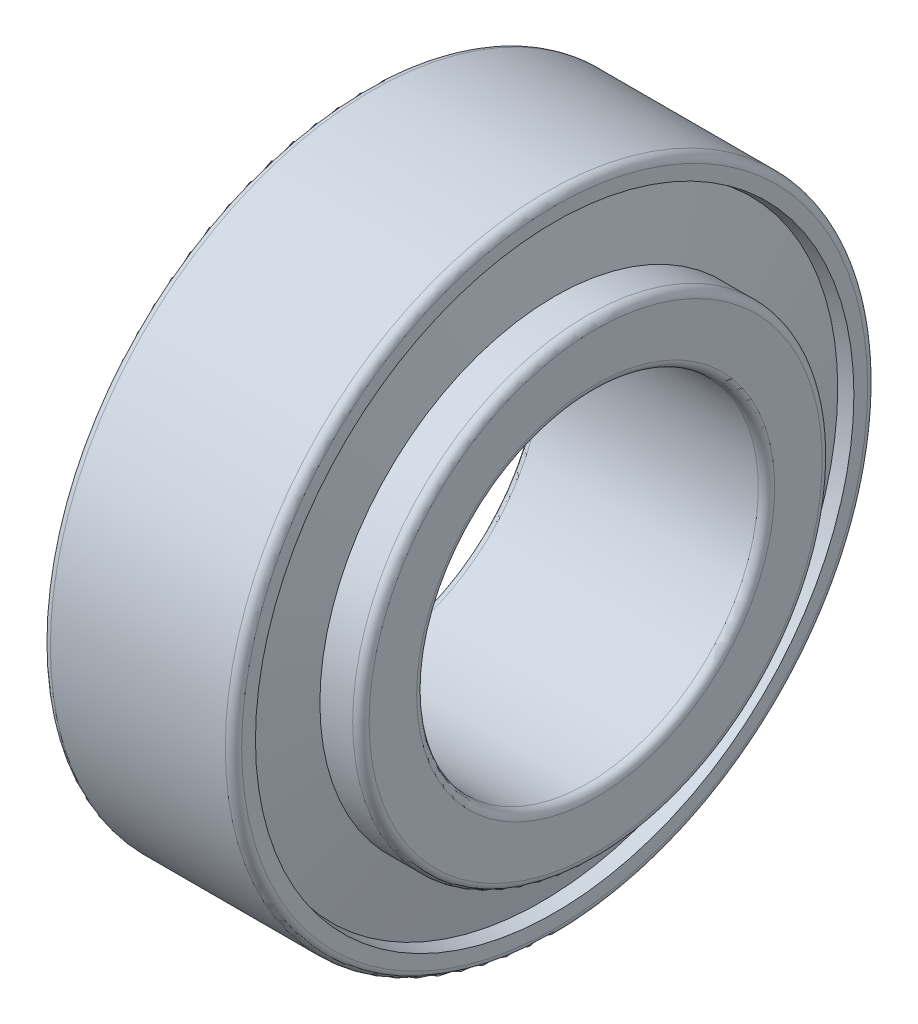
SolidWorks part; units mm, degrees
material "AISI Тип A2 Инструментальная сталь"
ref_plane "Спереди" through (0, 0, 0) normal (0, 0, 1) x (1, 0, 0)
ref_plane "Сверху" through (0, 0, 0) normal (0, 1, 0) x (1, 0, 0)
ref_plane "Справа" through (0, 0, 0) normal (1, 0, 0) x (0, 0, -1)
sketch "Эскиз1" plane through (0, 0, 0) normal (0, 0, 1) x (1, 0, 0)
  line L20 (-882.5277, 0) -> (43243.8573, 0) construction
  line L33 (0.9702, 19.3299) -> (0, 19.139)
  line L34 (0, 19.139) -> (0, 22.9)
  line L35 (0.6, 23.5) -> (13.4, 23.5)
  line L36 (14, 22.9) -> (14, 21.8935)
  line L37 (14, 21.8935) -> (13.0124, 21.6992)
  line L38 (0.9702, 19.3299) -> (13.0124, 21.6992) construction
  line L39 (1.9404, 14.2996) -> (0, 14.2996)
  line L40 (0, 14.2996) -> (0, 13.1)
  line L41 (0.6, 12.5) -> (16.4, 12.5)
  line L42 (17, 13.1) -> (17, 16.5788)
  line L43 (16.4, 17.1788) -> (14, 17.1788)
  line L44 (14, 17.1788) -> (14, 16.5788)
  line L45 (1.9404, 14.2996) -> (14, 16.5788) construction
  line L46 (14, 16.5788) -> (13.0124, 21.6992)
  line L47 (1.9404, 14.2996) -> (0.9702, 19.3299)
  line L48 (1.4553, 16.8147) -> (13.5062, 19.139) construction
  line L49 (0, 19.139) -> (13.5062, 19.139) construction
  line L50 (0.9702, 19.3299) -> (0.9702, 14.2996) construction
  arc A0 (0, 22.9) -> (0.6, 23.5) centre (0.6, 22.9) cw
  arc A1 (13.4, 23.5) -> (14, 22.9) centre (13.4, 22.9) cw
  arc A2 (0, 13.1) -> (0.6, 12.5) centre (0.6, 13.1) ccw
  arc A3 (17, 13.1) -> (16.4, 12.5) centre (16.4, 13.1) cw
  arc A4 (16.4, 17.1788) -> (17, 16.5788) centre (16.4, 16.5788) cw
  point P12 (13.5062, 19.139)
  dimension "гост r1" = 0.6
  dimension "гост r2" = 0.6
  dimension "гост DD" = 47
  dimension "гост B" = 17
  dimension "гост C" = 14
  dimension "гост T" = 17
  dimension "гост E" = 38.278
  dimension "гост d" = 25
  dimension "гост alfa" = 10.917
revolve "Повернуть1" add sketch "Эскиз1" angle 360 about L20
